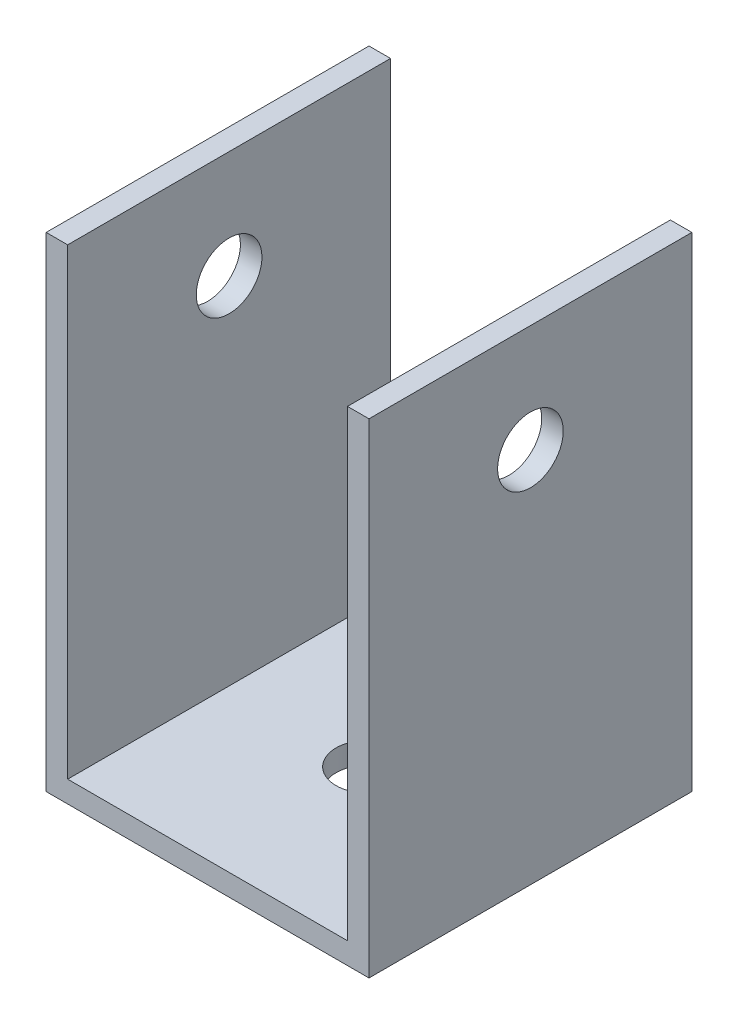
SolidWorks part; units mm, degrees
material "6061 合金"
ref_plane "前视基准面" through (0, 0, 0) normal (0, 0, 1) x (1, 0, 0)
ref_plane "上视基准面" through (0, 0, 0) normal (0, 1, 0) x (1, 0, 0)
ref_plane "右视基准面" through (0, 0, 0) normal (1, 0, 0) x (0, 0, -1)
sketch "草图1" plane through (0, 0, 0) normal (0, 0, 1) x (1, 0, 0)
  line L0 (-21.2901, 15.2018) -> (22.7584, 15.2018) construction
  line L1 (-15, 37.7018) -> (-13, 37.7018)
  line L2 (-15, 37.7018) -> (-15, -7.2982)
  line L3 (-15, -7.2982) -> (15, -7.2982)
  line L4 (15, 37.7018) -> (15, -7.2982)
  line L5 (0, 17.058) -> (0, -22.1538) construction
  line L6 (-13, 37.7018) -> (-13, -5.2982)
  line L7 (-13, -5.2982) -> (13, -5.2982)
  line L8 (13, -5.2982) -> (13, 37.7018)
  line L9 (13, 37.7018) -> (15, 37.7018)
  dimension "D1" = 2
  dimension "D2" = 2
  dimension "D3" = 45
  dimension "D4" = 30
extrude "凸台-拉伸1" add sketch "草图1" along normal blind 30
sketch "草图2" plane through (0, 0, 0) normal (0, 1, 0) x (1, 0, 0)
  line L0 (-24.1875, -15) -> (24.0648, -15) construction
  line L1 (13, 0) -> (-13, 0) construction
  line L2 (0, 11.2505) -> (0, -37.2429) construction
  line L3 (13, -30) -> (-13, -30) construction
  line L4 (-15, -30) -> (-15, 0) construction
  line L5 (15, -30) -> (15, 0) construction
  circle A0 centre (0, -15) radius 3.05
  dimension "D1" = 6.1
extrude "切除-拉伸1" cut sketch "草图2" against normal blind 30
sketch "草图3" plane through (-15, 0, 0) normal (-1, 0, 0) x (0, 0, 1)
  line L0 (15, 23.7518) -> (15, -8.7572) construction
  line L1 (0, 37.7018) -> (0, -7.2982) construction
  line L2 (30, 37.7018) -> (30, -7.2982) construction
  line L4 (30, -7.2982) -> (0, -7.2982) construction
  circle A0 centre (15, 27.7018) radius 3.05
  dimension "D1" = 6.1
  dimension "D2" = 35
extrude "切除-拉伸2" cut sketch "草图3" against normal blind 38
